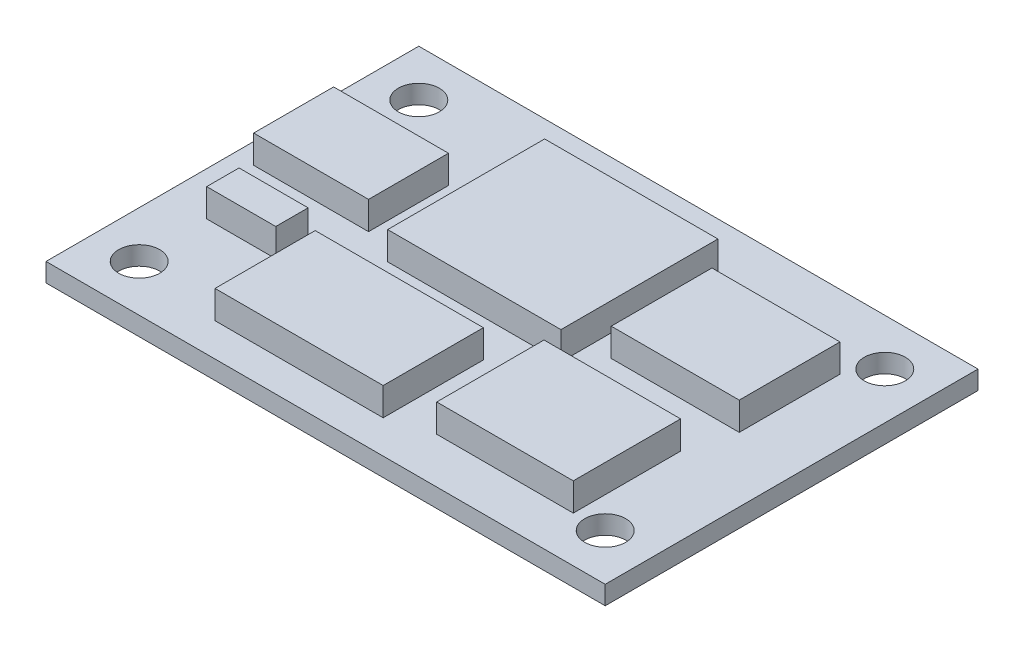
SolidWorks part; units mm, degrees
ref_plane "Front Plane" through (0, 0, 0) normal (0, 0, 1) x (1, 0, 0)
ref_plane "Top Plane" through (0, 0, 0) normal (0, 1, 0) x (1, 0, 0)
ref_plane "Right Plane" through (0, 0, 0) normal (1, 0, 0) x (0, 0, -1)
sketch "Sketch1" plane through (0, 0, 0) normal (0, 1, 0) x (1, 0, 0)
  line L0 (0, 13.8452) -> (0, -17.9531) construction
  line L1 (18.2573, 0) -> (-20.0831, 0) construction
  line L3 (30, -20) -> (-30, -20)
  line L4 (30, -20) -> (30, 20)
  line L5 (30, 20) -> (-30, 20)
  line L6 (-30, -20) -> (-30, 20)
  line L7 (30, -20) -> (-30, 20) construction
  line L8 (30, 20) -> (-30, -20) construction
  point P1 (0, 0)
  dimension "D1" = 60
  dimension "D2" = 40
extrude "Boss-Extrude1" add sketch "Sketch1" along normal blind 2
sketch "Sketch2" plane through (0, 2, 0) normal (0, 1, 0) x (1, 0, 0)
  line L1 (-15.4625, 8.6459) -> (-27.7888, 8.6459)
  line L2 (-15.4625, 8.6459) -> (-15.4625, 0.0707)
  line L3 (-15.4625, 0.0707) -> (-27.7888, 0.0707)
  line L4 (-27.7888, 8.6459) -> (-27.7888, 0.0707)
  line L5 (-15.4625, 8.6459) -> (-27.7888, 0.0707) construction
  line L6 (-15.4625, 0.0707) -> (-27.7888, 8.6459) construction
  line L7 (23.0759, 12.1165) -> (9.3385, 12.1165)
  line L8 (23.0759, 12.1165) -> (23.0759, 1.3075)
  line L9 (23.0759, 1.3075) -> (9.3385, 1.3075)
  line L10 (9.3385, 12.1165) -> (9.3385, 1.3075)
  line L11 (23.0759, 12.1165) -> (9.3385, 1.3075) construction
  line L12 (23.0759, 1.3075) -> (9.3385, 12.1165) construction
  line L13 (6.962, 15.1334) -> (-11.6308, 15.1334)
  line L14 (6.962, 15.1334) -> (6.962, -1.7094)
  line L15 (6.962, -1.7094) -> (-11.6308, -1.7094)
  line L16 (-11.6308, 15.1334) -> (-11.6308, -1.7094)
  line L17 (6.962, 15.1334) -> (-11.6308, -1.7094) construction
  line L18 (6.962, -1.7094) -> (-11.6308, 15.1334) construction
  line L19 (-17.9199, -3.9565) -> (-25.3315, -3.9565)
  line L20 (-17.9199, -3.9565) -> (-17.9199, -7.4277)
  line L21 (-17.9199, -7.4277) -> (-25.3315, -7.4277)
  line L22 (-25.3315, -3.9565) -> (-25.3315, -7.4277)
  line L23 (-17.9199, -3.9565) -> (-25.3315, -7.4277) construction
  line L24 (-17.9199, -7.4277) -> (-25.3315, -3.9565) construction
  line L25 (7.0191, -3.5839) -> (21.674, -3.5839)
  line L26 (7.0191, -3.5839) -> (7.0191, -15.0978)
  line L27 (7.0191, -15.0978) -> (21.674, -15.0978)
  line L28 (21.674, -3.5839) -> (21.674, -15.0978)
  line L29 (7.0191, -3.5839) -> (21.674, -15.0978) construction
  line L30 (7.0191, -15.0978) -> (21.674, -3.5839) construction
  line L31 (2.6187, -5.6921) -> (-15.4249, -5.6921)
  line L32 (2.6187, -5.6921) -> (2.6187, -16.4405)
  line L33 (2.6187, -16.4405) -> (-15.4249, -16.4405)
  line L34 (-15.4249, -5.6921) -> (-15.4249, -16.4405)
  line L35 (2.6187, -5.6921) -> (-15.4249, -16.4405) construction
  line L36 (2.6187, -16.4405) -> (-15.4249, -5.6921) construction
  point P0 (-21.6257, 4.3583)
  point P5 (16.2072, 6.712)
  point P10 (-2.3344, 6.712)
  point P15 (-21.6257, -5.6921)
  point P20 (14.3466, -9.3409)
  point P25 (-6.4031, -11.0663)
extrude "Boss-Extrude2" add sketch "Sketch2" along normal blind 3
hole_wizard "Ø4.4 (4.4) Diameter Hole1" positions "Sketch4" profile "Sketch3" hole size "Ø4.4" standard "ANSI Metric" end condition through all
sketch "Sketch4" plane through (0, 2, 0) normal (0, 1, 0) x (1, 0, 0)
  line L0 (25, 15) -> (25, -15) construction
  line L1 (25, -15) -> (-25, -15) construction
  line L2 (-25, -15) -> (-25, 15) construction
  line L3 (-25, 15) -> (25, 15) construction
  line L6 (-30, 20) -> (-30, -20) construction
  line L7 (-30, -20) -> (30, -20) construction
  point P0 (-25, 15)
  point P2 (25, 15)
  point P4 (25, -15)
  point P6 (-25, -15)
  dimension "D1" = 30
  dimension "D2" = 50
  dimension "D3" = 5
  dimension "D4" = 5
sketch "Sketch3" plane through (-25, 2, -15) normal (1, 0, 0) x (0, 0, 1)
  line L0 (0, 0) -> (0, 2)
  line L1 (0, 2) -> (2.2, 2)
  line L2 (2.2, 2) -> (2.2, 0)
  line L5 (2.2, 0) -> (0, 0)
  line L11 (0, -6.35) -> (0, 107.95) construction
  dimension "Thru Hole Dia." = 4.4
  dimension "Thru Hole Depth" = 2
